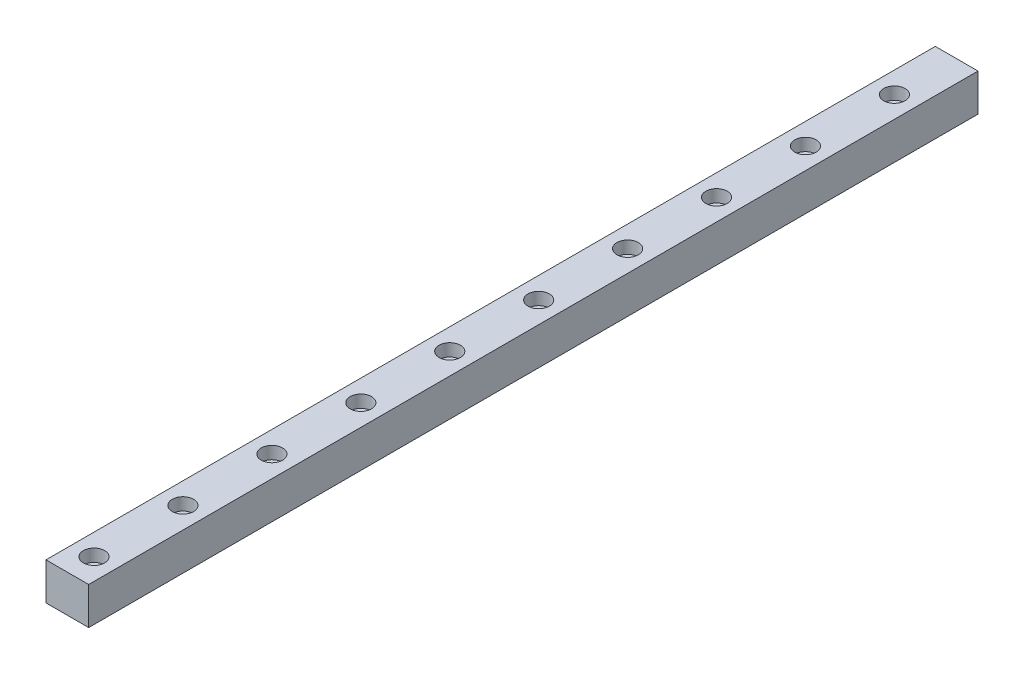
SolidWorks part; units mm, degrees
ref_plane "Front Plane" through (0, 0, 0) normal (0, 0, 1) x (1, 0, 0)
ref_plane "Top Plane" through (0, 0, 0) normal (0, 1, 0) x (1, 0, 0)
ref_plane "Right Plane" through (0, 0, 0) normal (1, 0, 0) x (0, 0, -1)
sketch "Sketch1" plane through (0, 0, 0) normal (0, 0, 1) x (1, 0, 0)
  line L1 (0, 0) -> (12, 0)
  line L2 (0, 0) -> (0, 10.5)
  line L3 (0, 10.5) -> (12, 10.5)
  line L4 (12, 0) -> (12, 10.5)
  dimension "D1" = 10.5
  dimension "D2" = 12
extrude "Boss-Extrude1" add sketch "Sketch1" along normal blind 250
sketch "Sketch2" plane through (0, 10.5, 0) normal (0, 1, 0) x (1, 0, 0)
  line L0 (6, 0) -> (6, -250) construction
  line L1 (12, 0) -> (0, 0) construction
  line L2 (12, -250) -> (0, -250) construction
  line L3 (0, -242.5) -> (12, -242.5) construction
  line L4 (0, -250) -> (0, 0) construction
  line L5 (12, -250) -> (12, 0) construction
  circle A0 centre (6, -242.5) radius 3
  dimension "D2" = 6
  dimension "D1" = 7.5
extrude "Cut-Extrude1" cut sketch "Sketch2" against normal blind 3.5
sketch "Sketch3" plane through (0, 7, 0) normal (0, 1, 0) x (1, 0, 0)
  circle A0 centre (6, -242.5) radius 1.75
  dimension "D1" = 3.5
extrude "Cut-Extrude2" cut sketch "Sketch3" against normal through all
pattern_linear "LPattern1" count 12 spacing 25 along (0, 0, -1) of "Cut-Extrude2", "Cut-Extrude1"
